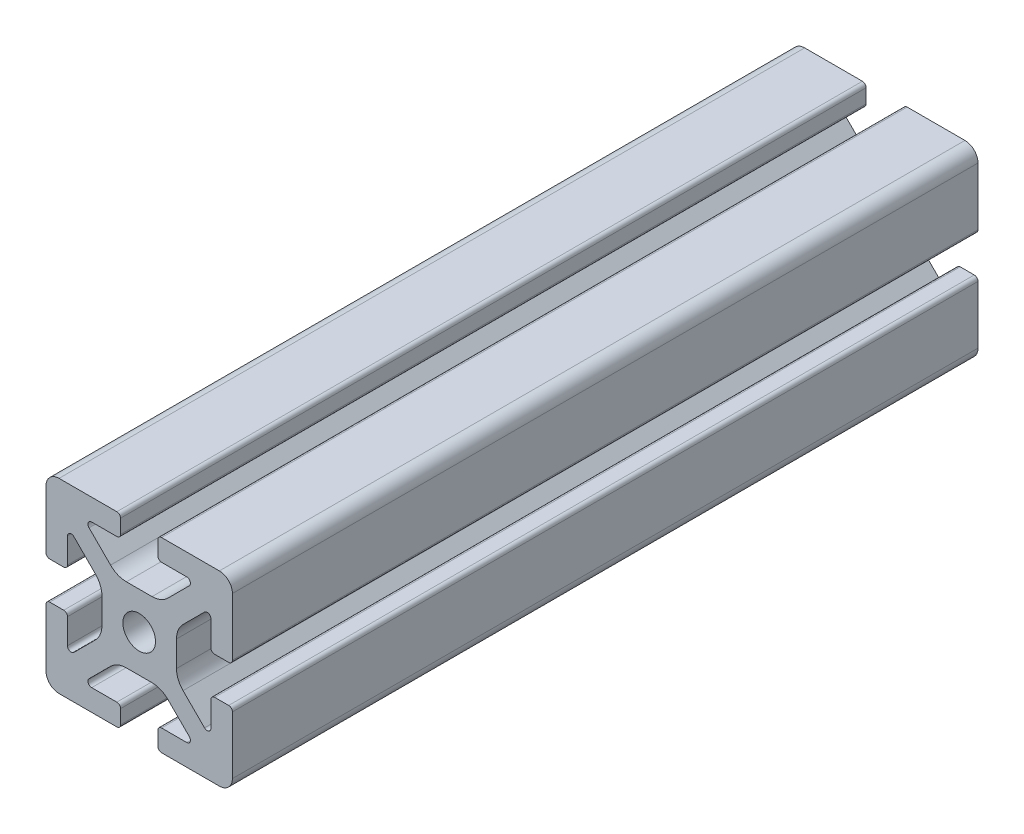
SolidWorks part; units mm, degrees
material "6061-T6 (SS)"
ref_plane "Front Plane" through (0, 0, 0) normal (0, 0, 1) x (1, 0, 0)
ref_plane "Top Plane" through (0, 0, 0) normal (0, 1, 0) x (1, 0, 0)
ref_plane "Right Plane" through (0, 0, 0) normal (1, 0, 0) x (0, 0, -1)
sketch "Sketch2" plane through (0, 0, 0) normal (0, 0, 1) x (1, 0, 0)
  line L0 (0, 20) -> (0, -20) construction
  line L1 (-20, 0) -> (20, 0) construction
  line L2 (4, -20) -> (20, -20)
  line L3 (20, -20) -> (20, -4)
  line L4 (4, -20) -> (4, -15.3907)
  line L5 (4, -15.3907) -> (12.1314, -15.3907)
  line L6 (12.1314, -15.3907) -> (4.7407, -8)
  line L7 (0, 0) -> (20, -20) construction
  line L8 (20, -4) -> (15.3907, -4)
  line L9 (15.3907, -4) -> (15.3907, -12.1314)
  line L10 (15.3907, -12.1314) -> (8, -4.7407)
  line L11 (11.6953, -8.436) -> (8.436, -11.6953) construction
  circle A0 centre (0, 0) radius 3.5
  arc A1 (10.2, -15.3907) -> (10.7657, -14.025) centre (10.2, -14.5907) ccw construction
  point P8 (0, -8)
  point P16 (10.0657, -10.0657)
  dimension "Center Hole Diameter" = 7
  dimension "D3" = 0.8
  dimension "Rail Height" = 40
  dimension "Rail Width" = 40
  dimension "T-Slot Width" = 8
  dimension "Slot Depth" = 12
  dimension "Slot Inner Width" = 22
sketch "Sketch3" plane through (0, 0, 0) normal (1, 0, 0) x (0, 0, -1)
  line L0 (-457.2, -20) -> (457.2, -20) construction
  line L1 (-431.8, 0) -> (431.8, 0) construction
  line L2 (0, 20) -> (0, -20) construction
  line L3 (0, 20) -> (0, -20) construction
  point P6 (-431.8, 0)
  point P8 (431.8, 0)
  dimension "Length" = 914.4
  dimension "D1" = 25.4
sketch "Sketch4" plane through (0, 0, 0) normal (0, 0, 1) x (1, 0, 0)
  line L0 (4.8, -20) -> (17.2, -20)
  line L1 (4, -20) -> (20, -20) construction
  line L2 (4, -20) -> (4, -15.3907) construction
  line L3 (4, -15.3907) -> (12.1314, -15.3907) construction
  line L4 (4, -16.1907) -> (4, -19.2)
  line L5 (4.8, -15.3907) -> (10.2, -15.3907)
  line L6 (0, -8) -> (2.7525, -8)
  line L7 (12.1314, -15.3907) -> (4.7407, -8) construction
  line L8 (6.1466, -9.4059) -> (10.7657, -14.025)
  line L9 (20, -20) -> (20, -4) construction
  line L10 (15.3907, -12.1314) -> (8, -4.7407) construction
  line L11 (15.3907, -4) -> (15.3907, -12.1314) construction
  line L12 (15.3907, -10.2) -> (15.3907, -4.8)
  line L13 (20, -4) -> (15.3907, -4) construction
  line L14 (16.1907, -4) -> (19.2, -4)
  line L15 (20, -4.8) -> (20, -17.2)
  line L16 (14.025, -10.7657) -> (9.4059, -6.1466)
  line L17 (8, 0) -> (8, -2.7525)
  line L18 (-20, 0) -> (20, 0) construction
  line L19 (0, -8) -> (0, -3.5)
  line L20 (0, 20) -> (0, -20) construction
  line L21 (8, 0) -> (3.5, 0)
  arc A0 (4, -19.2) -> (4.8, -20) centre (4.8, -19.2) ccw
  arc A1 (10.2, -15.3907) -> (10.7657, -14.025) centre (10.2, -14.5907) ccw construction
  arc A2 (4, -16.1907) -> (4.8, -15.3907) centre (4.8, -16.1907) cw
  arc A3 (10.2, -15.3907) -> (10.7657, -14.025) centre (10.2, -14.5907) ccw
  arc A4 (2.7525, -8) -> (6.1466, -9.4059) centre (2.7525, -12.8) cw
  arc A5 (17.2, -20) -> (20, -17.2) centre (17.2, -17.2) ccw
  arc A6 (14.025, -10.7657) -> (15.3907, -10.2) centre (14.5907, -10.2) ccw
  arc A7 (15.3907, -4.8) -> (16.1907, -4) centre (16.1907, -4.8) cw
  arc A8 (19.2, -4) -> (20, -4.8) centre (19.2, -4.8) cw
  arc A9 (9.4059, -6.1466) -> (8, -2.7525) centre (12.8, -2.7525) cw
  circle A10 centre (0, 0) radius 3.5 construction
  arc A11 (0, -3.5) -> (3.5, 0) centre (0, 0) ccw
  dimension "D1" = 2.8
  dimension "D2" = 4.8
extrude "Boss-Extrude1" add sketch "Sketch4" along normal mid plane 160
mirror "Mirror1" about plane through (0, 0, 0) normal (1, 0, 0) of bodies 134
mirror "Mirror2" about plane through (0, 0, 0) normal (0, 1, 0) of bodies 135
equation "\"D3@Sketch2\"=\"T-Slot Width@Sketch2\"*0.1"
equation "\"D1@Sketch4\"=\"D3@Sketch2\"*3.5"
equation "\"D2@Sketch4\"=\"D3@Sketch2\"*6"
equation "\"D1@Boss-Extrude1\"=\"Length@Sketch3\""
